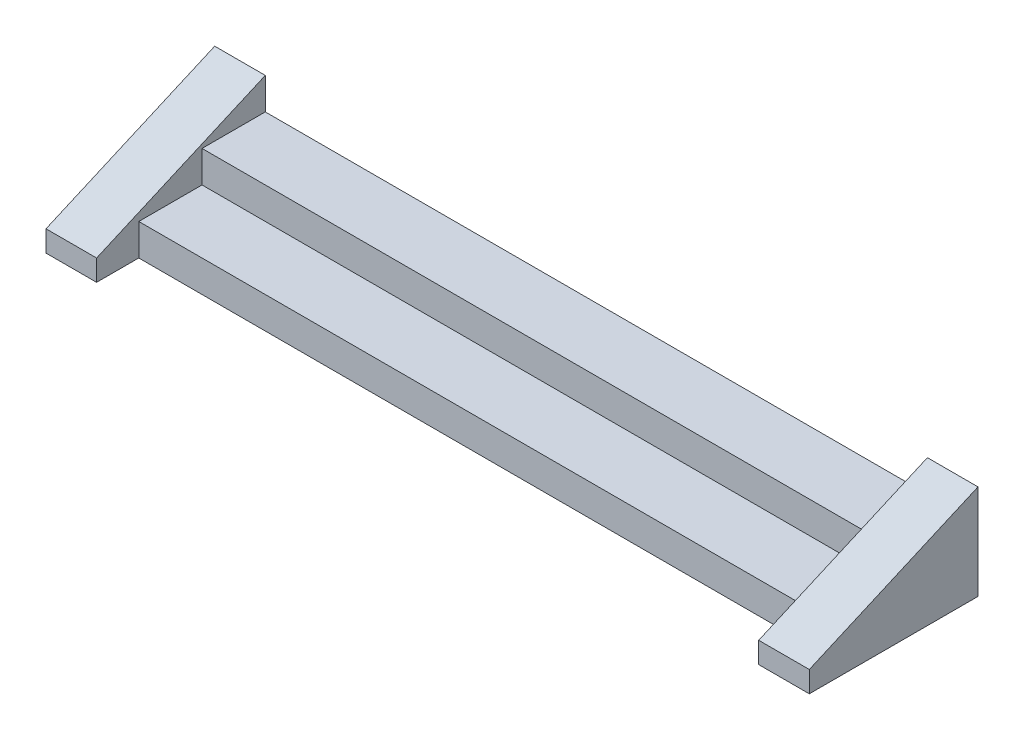
SolidWorks part; units mm, degrees
ref_plane "前视基准面" through (0, 0, 0) normal (0, 0, 1) x (1, 0, 0)
ref_plane "上视基准面" through (0, 0, 0) normal (0, 1, 0) x (1, 0, 0)
ref_plane "右视基准面" through (0, 0, 0) normal (1, 0, 0) x (0, 0, -1)
sketch "草图1" plane through (0, 0, 0) normal (1, 0, 0) x (0, 0, -1)
  line L0 (440.146, 300) -> (440.146, 0)
  line L1 (440.146, 0) -> (-159.854, 0)
  line L2 (-159.854, 0) -> (-159.854, 150)
  line L3 (-159.854, 150) -> (140.146, 150)
  line L4 (140.146, 150) -> (140.146, 300)
  line L5 (140.146, 300) -> (440.146, 300)
  dimension "D1" = 150
  dimension "D2" = 150
  dimension "D3" = 600
  dimension "D4" = 300
extrude "凸台-拉伸1" add sketch "草图1" along normal blind 3300
sketch "草图2" plane through (3300, 0, 0) normal (1, 0, 0) x (0, 0, -1)
  line L0 (440.146, 450) -> (-359.854, 100)
  line L1 (-359.854, 100) -> (-359.854, 0)
  line L2 (-359.854, 0) -> (440.146, 0)
  line L3 (440.146, 0) -> (440.146, 450)
  dimension "D1" = 200
  dimension "D2" = 150
  dimension "D3" = 100
extrude "凸台-拉伸2" add sketch "草图2" along normal blind 240
sketch "草图3" plane through (0, 0, 0) normal (-1, 0, 0) x (0, 0, 1)
  line L0 (-440.146, 300) -> (-440.146, 0)
  line L1 (-440.146, 0) -> (159.854, 0)
  line L2 (159.854, 0) -> (159.854, 150)
  line L3 (159.854, 150) -> (-140.146, 150)
  line L4 (-140.146, 150) -> (-140.146, 300)
  line L5 (-140.146, 300) -> (-440.146, 300)
extrude "切除-拉伸1" cut sketch "草图3" against normal blind 160
sketch "草图4" plane through (160, 0, 0) normal (-1, 0, 0) x (0, 0, 1)
  line L0 (-440.146, 450) -> (-440.146, 0)
  line L1 (-440.146, 0) -> (359.854, 0)
  line L2 (359.854, 0) -> (359.854, 100)
  line L3 (359.854, 100) -> (-440.146, 450)
extrude "凸台-拉伸3" add sketch "草图4" along normal blind 240
